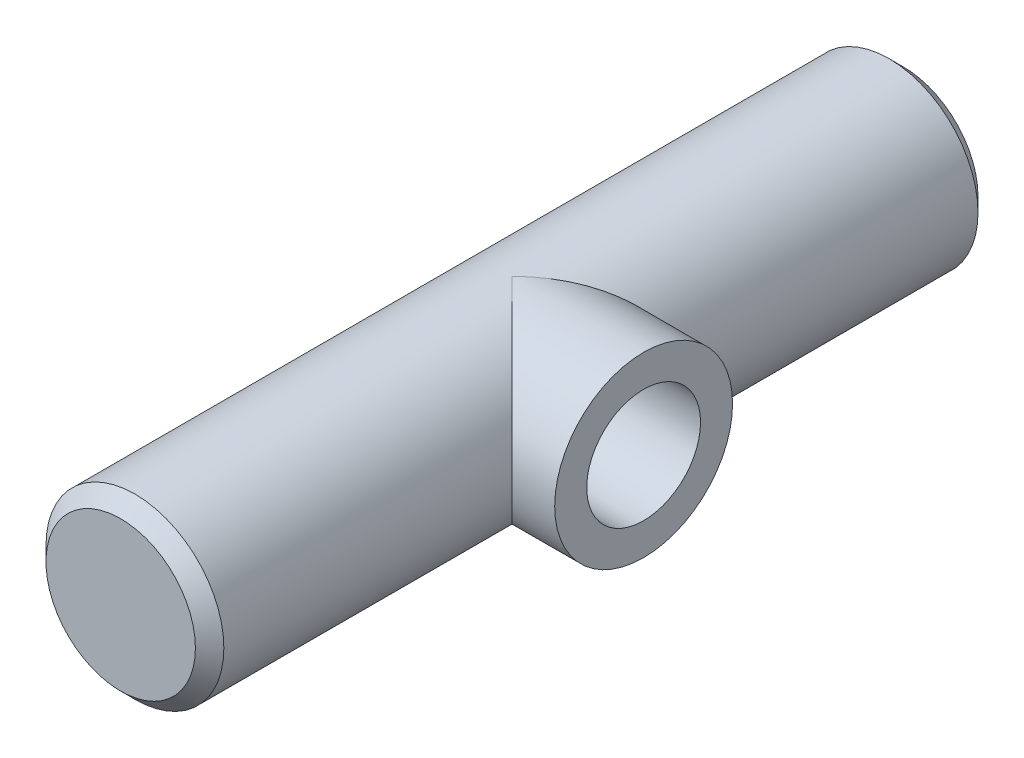
SolidWorks part; units mm, degrees
other "Weld Folder"
material "AISI 1020 Steel, Cold Rolled"
ref_plane "Front Plane" through (0, 0, 0) normal (0, 0, 1) x (1, 0, 0)
ref_plane "Top Plane" through (0, 0, 0) normal (0, 1, 0) x (1, 0, 0)
ref_plane "Right Plane" through (0, 0, 0) normal (1, 0, 0) x (0, 0, -1)
sketch "Sketch3" plane through (0, 0, 0) normal (0, 0, 1) x (1, 0, 0)
  circle A0 centre (0, 0) radius 12.5
  dimension "D1" = 25
extrude "Boss-Extrude1" add sketch "Sketch3" along normal blind 110
sketch "Sketch4" plane through (0, 0, 0) normal (1, 0, 0) x (0, 0, -1)
  line L0 (-110, 12.5) -> (-110, -12.5) construction
  circle A0 centre (-55, 0) radius 12.5
  dimension "D1" = 25
  dimension "D2" = 55
extrude "Boss-Extrude2" add sketch "Sketch4" along normal blind 18.5
sketch "Sketch5" plane through (18.5, 0, 0) normal (1, 0, 0) x (0, 0, -1)
  circle A0 centre (-55, 0) radius 8
  dimension "D1" = 16
chamfer "Chamfer1" distance 2 angle 45
extrude "Cut-Extrude1" cut sketch "Sketch5" against normal blind 18.5
